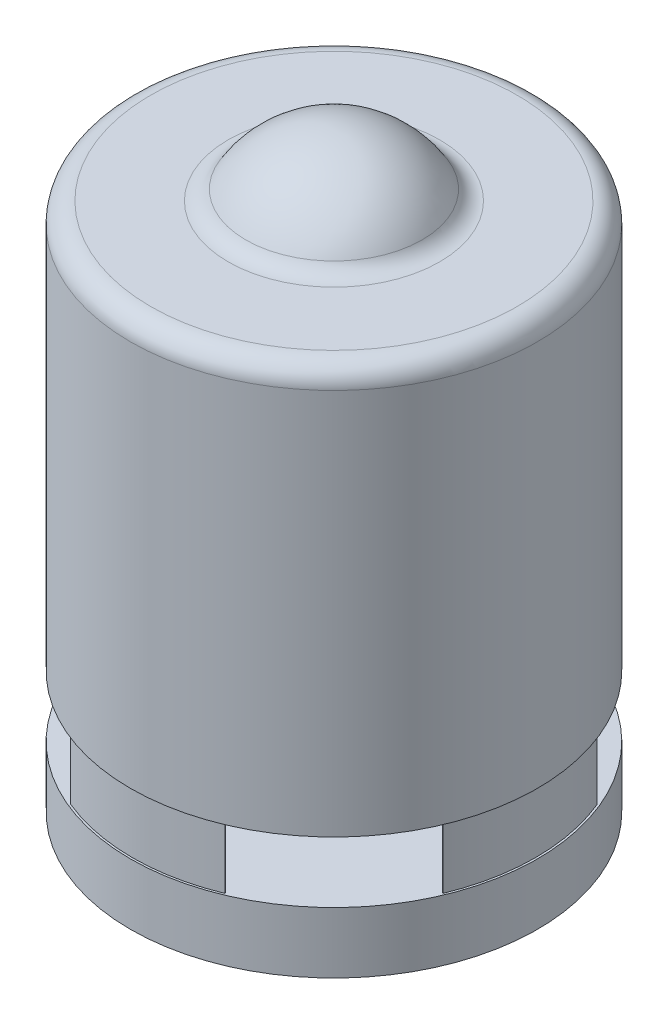
SolidWorks part; units mm, degrees
material "Thornel VCB-20 Carbon Cloth"
ref_plane "Front Plane" through (0, 0, 0) normal (0, 0, 1) x (1, 0, 0)
ref_plane "Top Plane" through (0, 0, 0) normal (0, 1, 0) x (1, 0, 0)
ref_plane "Right Plane" through (0, 0, 0) normal (1, 0, 0) x (0, 0, -1)
sketch "Sketch1" plane through (0, 0, 0) normal (0, 1, 0) x (1, 0, 0)
  circle A0 centre (0, 0) radius 100
  dimension "D1" = 200
extrude "Boss-Extrude1" add sketch "Sketch1" along normal blind 30
sketch "Sketch2" plane through (0, 30, 0) normal (0, 1, 0) x (1, 0, 0)
  line L0 (0, 0) -> (144.1325, 0) construction
  line L1 (0, 0) -> (155.8211, 64.5432) construction
  line L2 (91.4641, 37.8857) -> (91.0021, 37.6943)
  line L3 (155.8211, -64.5432) -> (0, 0) construction
  line L4 (91.4641, -37.8857) -> (91.0021, -37.6943)
  line L5 (37.8857, -91.4641) -> (37.6943, -91.0021)
  line L6 (-37.8857, -91.4641) -> (-37.6943, -91.0021)
  line L7 (-91.4641, -37.8857) -> (-91.0021, -37.6943)
  line L8 (-91.4641, 37.8857) -> (-91.0021, 37.6943)
  line L9 (-37.8857, 91.4641) -> (-37.6943, 91.0021)
  line L10 (37.8857, 91.4641) -> (37.6943, 91.0021)
  arc A0 (91.4641, 37.8857) -> (91.4641, -37.8857) centre (0, 0) cw
  arc A1 (91.0021, 37.6943) -> (91.0021, -37.6943) centre (0, 0) cw
  arc A2 (37.8857, -91.4641) -> (-37.8857, -91.4641) centre (0, 0) cw
  arc A3 (37.6943, -91.0021) -> (-37.6943, -91.0021) centre (0, 0) cw
  arc A4 (-91.4641, -37.8857) -> (-91.4641, 37.8857) centre (0, 0) cw
  arc A5 (-91.0021, -37.6943) -> (-91.0021, 37.6943) centre (0, 0) cw
  arc A6 (-37.8857, 91.4641) -> (37.8857, 91.4641) centre (0, 0) cw
  arc A7 (-37.6943, 91.0021) -> (37.6943, 91.0021) centre (0, 0) cw
  point P24 (0, 0)
  dimension "D3" = 99
  dimension "D4" = 98.5
  dimension "D1" = 22.5
  dimension "D2" = 45
  dimension "D5" = 4
extrude "Boss-Extrude2" add sketch "Sketch2" along normal blind 30
ref_plane "Plane1" through (0, 60, 0) normal (0, 1, 0) x (1, 0, 0)
sketch "Sketch3" plane through (0, 60, 0) normal (0, 1, 0) x (1, 0, 0)
  circle A0 centre (0, 0) radius 100
  dimension "D1" = 200
extrude "Boss-Extrude3" add sketch "Sketch3" along normal blind 200
sketch "Sketch5" plane through (0, 0, 0) normal (0, 0, 1) x (1, 0, 0)
  line L0 (0, 115.7285) -> (0, 316.9271) construction
  line L1 (100, 260) -> (-100, 260) construction
  line L2 (45.8258, 260) -> (0, 260)
  line L3 (0, 260) -> (0, 290)
  arc A0 (0, 290) -> (45.8258, 260) centre (0, 240) cw
  dimension "D1" = 50
  dimension "D2" = 240
revolve "Revolve1" add sketch "Sketch5" angle 360 about L0
fillet "Fillet1" radius 10 2 edges at (0, 260, 100) (0, 260, 45.8258)
scale "Scale1" scale about centroid uniform scaling yes scale factor 0.233333
